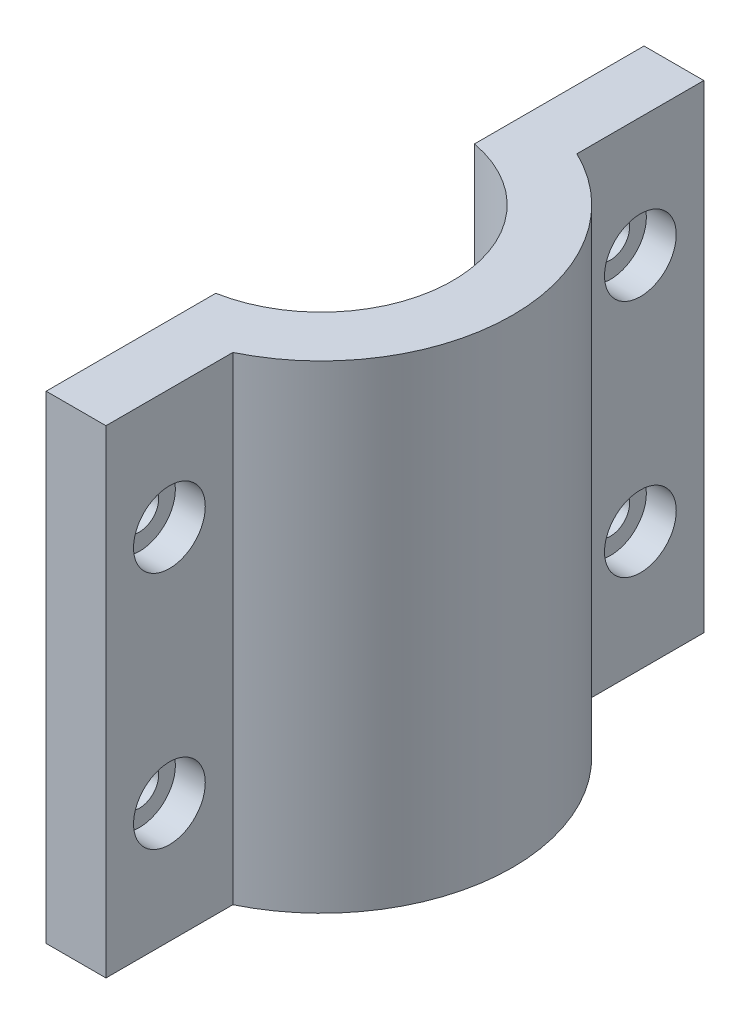
SolidWorks part; units mm, degrees
ref_plane "Front Plane" through (0, 0, 0) normal (0, 0, 1) x (1, 0, 0)
ref_plane "Top Plane" through (0, 0, 0) normal (0, 1, 0) x (1, 0, 0)
ref_plane "Right Plane" through (0, 0, 0) normal (1, 0, 0) x (0, 0, -1)
sketch "Sketch1" plane through (0, 0, 0) normal (0, 1, 0) x (1, 0, 0)
  line L0 (6.35, 25.4) -> (6.35, 25.4)
  line L3 (6.35, 18.2721) -> (6.35, 25.4)
  line L8 (0, 13.7372) -> (0, 31.75)
  line L9 (0, 31.75) -> (6.35, 31.75)
  line L10 (6.35, -18.2721) -> (6.35, -25.4)
  line L11 (0, -13.7372) -> (0, -31.75)
  line L12 (0, -31.75) -> (6.35, -31.75)
  line L13 (6.35, -25.4) -> (6.35, -25.4)
  line L14 (-2.54, 0) -> (0, 0) construction
  line L15 (6.35, -31.75) -> (6.35, -25.4)
  line L16 (6.35, 31.75) -> (6.35, 25.4)
  arc A2 (0, 13.7372) -> (0, -13.7372) centre (-2.54, 0) cw
  arc A3 (6.35, 18.2721) -> (6.35, -18.2721) centre (-2.54, 0) cw
  dimension "D1" = 2.54
  dimension "D2" = 13.97
  dimension "D3" = 63.5
  dimension "D4" = 6.35
ref_plane "Plane1" through (0, 50.8, 0) normal (0, 1, 0) x (1, 0, 0)
extrude "Boss-Extrude1" add sketch "Sketch1" along normal up to surface (50.8 mm away) up to plane "Plane1"
ref_plane "Plane2" through (0, 25.4, 0) normal (0, 1, 0) x (1, 0, 0)
ref_plane "Plane3" through (3.175, 0, 0) normal (1, 0, 0) x (0, 0, -1)
sketch "Sketch2" plane through (6.35, 0, 0) normal (1, 0, 0) x (0, 0, -1)
  line L0 (25.0111, 50.8) -> (25.0111, 25.4) construction
  line L1 (18.2721, 50.8) -> (31.75, 50.8) construction
  line L3 (24.8499, 25.4) -> (-24.8499, 25.4) construction
  line L4 (0, 9.779) -> (0, -9.779) construction
  circle A0 centre (25.0111, 38.1) radius 2.032
  circle A1 centre (25.0111, 12.7) radius 2.032
  circle A2 centre (-25.0111, 12.7) radius 2.032
  circle A3 centre (-25.0111, 38.1) radius 2.032
  point P4 (25.0111, 25.4)
  point P8 (25.0111, 41.156)
  point P10 (25.0111, 40.3307)
  point P11 (25.0111, 43.4069)
  point P12 (25.0111, 38.1)
  dimension "D1" = 4.064
sketch "Sketch3" plane through (6.35, 0, 0) normal (1, 0, 0) x (0, 0, -1)
  line L0 (24.8499, 25.4) -> (-24.8499, 25.4) construction
  line L1 (0, 9.779) -> (0, -9.779) construction
  circle A0 centre (25.0111, 38.1) radius 3.81
  circle A1 centre (25.0111, 12.7) radius 3.81
  circle A3 centre (-25.0111, 38.1) radius 3.81
  circle A4 centre (-25.0111, 12.7) radius 3.81
  dimension "D1" = 7.62
extrude "Cut-Extrude1" cut sketch "Sketch2" against normal through all both and the other way through all
extrude "Cut-Extrude2" cut sketch "Sketch3" against normal up to surface (3.175 mm away)
